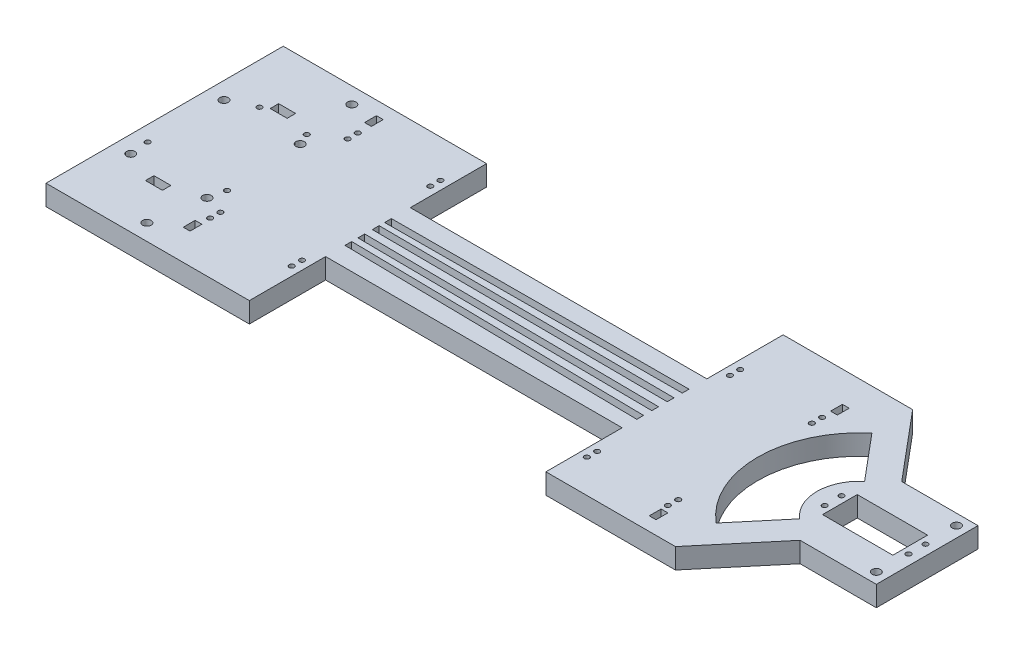
SolidWorks part; units mm, degrees
ref_plane "Front Plane" through (0, 0, 0) normal (0, 0, 1) x (1, 0, 0)
ref_plane "Top Plane" through (0, 0, 0) normal (0, 1, 0) x (1, 0, 0)
ref_plane "Right Plane" through (0, 0, 0) normal (1, 0, 0) x (0, 0, -1)
sketch "Sketch1" plane through (0, 0, 0) normal (0, 1, 0) x (1, 0, 0)
  line L0 (295, 140) -> (450, 140)
  line L1 (0, 0) -> (120, 0)
  line L2 (0, 0) -> (0, 140)
  line L3 (0, 140) -> (120, 140)
  line L4 (450, 0) -> (450, 140)
  line L6 (120, 140) -> (120, 95)
  line L7 (120, 95) -> (295, 95)
  line L8 (295, 140) -> (295, 95)
  line L10 (120, 0) -> (120, 45)
  line L11 (120, 45) -> (295, 45)
  line L12 (295, 0) -> (295, 45)
  line L13 (295, 0) -> (450, 0)
  line L14 (120, 83.84) -> (295, 84.455)
  line L15 (295, 84.455) -> (295, 80.455)
  line L16 (295, 80.455) -> (120, 79.84)
  line L17 (120, 79.84) -> (120, 83.84)
  line L18 (120, 76.59) -> (295, 75.595)
  line L19 (295, 75.595) -> (295, 71.595)
  line L20 (295, 71.595) -> (120, 72.59)
  line L21 (120, 72.59) -> (120, 76.59)
  line L22 (120, 68.09) -> (295, 66.495)
  line L23 (295, 66.495) -> (295, 62.495)
  line L24 (295, 62.495) -> (120, 64.09)
  line L25 (120, 64.09) -> (120, 68.09)
  line L26 (120, 60.42) -> (295, 57.635)
  line L27 (295, 57.635) -> (295, 53.635)
  line L28 (295, 53.635) -> (120, 56.42)
  line L29 (120, 56.42) -> (120, 60.42)
  line L30 (350, 140) -> (350, 0) construction
  line L31 (6.35, 104.3) -> (59.65, 104.3) construction
  line L32 (6.35, 104.3) -> (6.35, 35.7) construction
  line L33 (6.35, 35.7) -> (59.65, 35.7) construction
  line L34 (59.65, 104.3) -> (59.65, 35.7) construction
  line L35 (6, 112) -> (60, 112) construction
  line L36 (6, 112) -> (6, 28) construction
  line L37 (6, 28) -> (60, 28) construction
  line L38 (60, 112) -> (60, 28) construction
  line L39 (28, 104.3) -> (38, 104.3)
  line L40 (28, 104.3) -> (28, 109.3)
  line L41 (28, 109.3) -> (38, 109.3)
  line L42 (38, 104.3) -> (38, 109.3)
  line L43 (28, 35.7) -> (38, 35.7)
  line L44 (28, 35.7) -> (28, 30.7)
  line L45 (28, 30.7) -> (38, 30.7)
  line L46 (38, 35.7) -> (38, 30.7)
  line L47 (63, 132) -> (67, 132)
  line L48 (63, 132) -> (63, 125)
  line L49 (63, 125) -> (67, 125)
  line L50 (67, 132) -> (67, 125)
  line L51 (63, 25) -> (67, 25)
  line L52 (63, 25) -> (63, 18)
  line L53 (63, 18) -> (67, 18)
  line L54 (67, 25) -> (67, 18)
  line L56 (398.5, 80.25) -> (440, 80.25)
  line L57 (398.5, 80.25) -> (398.5, 59.75)
  line L58 (398.5, 59.75) -> (440, 59.75)
  line L59 (440, 80.25) -> (440, 59.75)
  line L60 (398.5, 80.25) -> (391.5, 80.25) construction
  line L61 (391.5, 80.25) -> (391.5, 59.75) construction
  line L62 (391.5, 59.75) -> (398.5, 59.75) construction
  line L63 (440, 59.75) -> (447, 59.75) construction
  line L64 (447, 59.75) -> (447, 80.25) construction
  line L65 (447, 80.25) -> (440, 80.25) construction
  line L66 (410, 80.25) -> (410, 59.75) construction
  line L67 (120, 81.84) -> (50119.6912, 257.5532) construction
  line L68 (393.9303, 50.8489) -> (371.4327, 24.0373)
  line L69 (393.9303, 89.1511) -> (371.4327, 115.9627)
  line L70 (120, 74.59) -> (50119.1918, -209.6911) construction
  line L71 (120, 66.09) -> (50117.9234, -389.6054) construction
  line L72 (120, 58.42) -> (50113.6696, -737.1935) construction
  line L73 (115.0463, 81.8226) -> (114.8605, 134.6962) construction
  line L74 (66.4466, 81.6518) -> (66.2773, 129.8225) construction
  line L75 (66.5944, 66.5768) -> (66.1224, 14.7918) construction
  line L76 (115.1924, 66.1338) -> (114.7306, 15.4677) construction
  line L77 (299.8782, 73.5673) -> (300.2267, 134.8495) construction
  line L78 (348.4774, 73.2909) -> (348.827, 134.7671) construction
  line L79 (300.1686, 55.5527) -> (299.5319, 15.545) construction
  line L80 (348.7624, 54.7794) -> (347.9619, 4.4785) construction
  line L82 (348, 122) -> (352, 122)
  line L83 (348, 122) -> (348, 115)
  line L84 (348, 115) -> (352, 115)
  line L85 (352, 122) -> (352, 115)
  line L86 (348, 15) -> (352, 15)
  line L87 (348, 15) -> (348, 8)
  line L88 (348, 8) -> (352, 8)
  line L89 (352, 15) -> (352, 8)
  circle A0 centre (8.95, 51) radius 1.5
  circle A1 centre (57.15, 49.7) radius 1.5
  circle A2 centre (24.15, 101.8) radius 1.5
  circle A3 centre (52.05, 101.8) radius 1.5
  circle A4 centre (50, 130.475) radius 2.5
  circle A5 centre (50, 9.525) radius 2.5
  circle A6 centre (10, 95) radius 2.5
  circle A7 centre (10, 40) radius 2.5
  circle A8 centre (55, 40) radius 2.5
  circle A9 centre (55, 95) radius 2.5
  arc A12 (371.4327, 115.9627) -> (371.4327, 24.0373) centre (410, 70) ccw
  arc A13 (393.9303, 89.1511) -> (393.9303, 50.8489) centre (410, 70) ccw
  circle A14 centre (394.5, 75) radius 1.5
  circle A15 centre (394.5, 65) radius 1.5
  circle A16 centre (444, 75) radius 1.5
  circle A17 centre (444, 65) radius 1.5
  circle A18 centre (114.9408, 111.8226) radius 1.5
  circle A19 centre (114.9198, 117.8226) radius 1.5
  circle A20 centre (66.3411, 111.6518) radius 1.5
  circle A21 centre (66.3201, 117.6518) radius 1.5
  circle A22 centre (114.919, 36.1338) radius 1.5
  circle A23 centre (114.8643, 30.1338) radius 1.5
  circle A24 centre (66.2663, 30.578) radius 1.5
  circle A25 centre (66.321, 36.578) radius 1.5
  circle A26 centre (300.0488, 103.5673) radius 1.5
  circle A27 centre (300.0829, 109.5673) radius 1.5
  circle A28 centre (348.6821, 109.2909) radius 1.5
  circle A29 centre (348.648, 103.2909) radius 1.5
  circle A30 centre (299.6911, 25.5527) radius 1.5
  circle A31 centre (299.5957, 19.5527) radius 1.5
  circle A32 centre (348.285, 24.7794) radius 1.5
  circle A33 centre (348.1895, 18.7794) radius 1.5
  point P27 (120, 81.84)
  point P30 (120, 74.59)
  point P31 (120, 66.09)
  point P32 (120, 58.42)
  point P33 (295, 82.455)
  point P35 (295, 73.595)
  point P36 (295, 64.495)
  point P37 (295, 55.635)
  point P41 (6.35, 70)
  point P46 (6, 70)
  point P47 (33, 28)
  point P50 (33, 35.7)
  point P61 (33, 112)
  point P62 (33, 109.3)
  point P79 (33, 30.7)
  point P88 (440, 70)
  point P121 (398.5, 70)
  point P156 (0, 0)
  dimension "D31" = 3
  dimension "D32" = 3
  dimension "D33" = 3
  dimension "D34" = 3
  dimension "D49" = 5
  dimension "D50" = 5
  dimension "D62" = 5
  dimension "D63" = 5
  dimension "D66" = 5
  dimension "D68" = 5
  dimension "D72" = 70
  dimension "D79" = 25
  dimension "D82" = 3
  dimension "D83" = 3
  dimension "D84" = 3
  dimension "D85" = 3
  dimension "D92" = 3
  dimension "D93" = 3
  dimension "D94" = 3
  dimension "D95" = 3
  dimension "D102" = 3
  dimension "D103" = 3
  dimension "D104" = 3
  dimension "D105" = 3
  dimension "D110" = 35
  dimension "D115" = 3
  dimension "D116" = 3
  dimension "D117" = 3
  dimension "D118" = 3
  dimension "D131" = 3
  dimension "D114" = 3
  dimension "D132" = 3
  dimension "D133" = 3
  dimension "D1" = 450
  dimension "D2" = 140
  dimension "D3" = 120
  dimension "D4" = 175
  dimension "D5" = 45
  dimension "D6" = 45
  dimension "D7" = 13.16
  dimension "D8" = 4
  dimension "D9" = 12.545
  dimension "D10" = 4
  dimension "D11" = 4
  dimension "D12" = 4
  dimension "D13" = 7.25
  dimension "D14" = 8.5
  dimension "D15" = 7.67
  dimension "D16" = 4
  dimension "D17" = 4
  dimension "D18" = 4
  dimension "D19" = 4
  dimension "D20" = 8.86
  dimension "D21" = 9.1
  dimension "D22" = 8.86
  dimension "D23" = 53.3
  dimension "D24" = 68.6
  dimension "D25" = 70
  dimension "D26" = 70
  dimension "D27" = 84
  dimension "D28" = 54
  dimension "D29" = 33
  dimension "D30" = 33
  dimension "D35" = 2.6
  dimension "D36" = 15.3
  dimension "D37" = 14
  dimension "D38" = 2.5
  dimension "D39" = 2.5
  dimension "D40" = 7.6
  dimension "D41" = 15.2
  dimension "D42" = 2.5
  dimension "D43" = 10
  dimension "D44" = 5
  dimension "D45" = 5
  dimension "D46" = 10
  dimension "D47" = 50
  dimension "D48" = 9.525
  dimension "D51" = 9.525
  dimension "D52" = 50
  dimension "D53" = 53
  dimension "D54" = 8
  dimension "D55" = 7
  dimension "D56" = 4
  dimension "D57" = 53
  dimension "D58" = 18
  dimension "D59" = 4
  dimension "D60" = 7
  dimension "D61" = 45
  dimension "D64" = 40
  dimension "D65" = 10
  dimension "D67" = 45
  dimension "D69" = 45
  dimension "D70" = 10
  dimension "D71" = 230
  dimension "D73" = 10
  dimension "D74" = 41.5
  dimension "D75" = 20.5
  dimension "D76" = 7
  dimension "D77" = 7
  dimension "D78" = 18.5
  dimension "D80" = 40
  dimension "D81" = 40
  dimension "D86" = 49.5
  dimension "D87" = 10
  dimension "D88" = 4
  dimension "D89" = 5
  dimension "D90" = 48.6
  dimension "D91" = 5
  dimension "D96" = 6
  dimension "D97" = 6
  dimension "D98" = 30
  dimension "D99" = 30
  dimension "D100" = 5
  dimension "D101" = 48.6
  dimension "D106" = 30
  dimension "D107" = 6
  dimension "D108" = 6
  dimension "D109" = 30
  dimension "D111" = 5
  dimension "D112" = 5
  dimension "D113" = 48.6
  dimension "D119" = 6
  dimension "D120" = 6
  dimension "D121" = 30
  dimension "D122" = 30
  dimension "D123" = 7
  dimension "D124" = 4
  dimension "D125" = 18
  dimension "D126" = 53
  dimension "D127" = 7
  dimension "D128" = 4
  dimension "D129" = 8
  dimension "D130" = 53
  dimension "D134" = 6
  dimension "D135" = 6
  dimension "D136" = 30
  dimension "D137" = 30
  dimension "D138" = 48.6
extrude "Boss-Extrude1" add sketch "Sketch1" along normal blind 12
sketch "Sketch2" plane through (0, 12, 0) normal (0, 1, 0) x (1, 0, 0)
  line L0 (371.4327, 140) -> (404.9967, 100)
  line L1 (450, 140) -> (295, 140) construction
  line L2 (450, 0) -> (450, 140) construction
  line L3 (393.9303, 89.1511) -> (371.4327, 115.9627) construction
  line L4 (371.4327, 0) -> (404.9967, 40)
  line L5 (295, 0) -> (450, 0) construction
  line L6 (371.4327, 24.0373) -> (393.9303, 50.8489) construction
  line L7 (450, 100) -> (404.9967, 100)
  line L8 (450, 40) -> (404.9967, 40)
  line L9 (371.4327, 140) -> (450, 140)
  line L10 (450, 140) -> (450, 100)
  line L11 (450, 40) -> (450, 0)
  line L12 (450, 0) -> (371.4327, 0)
  circle A0 centre (443.65, 93.65) radius 2.5
  circle A1 centre (443.65, 46.35) radius 2.5
  point P27 (0, 0)
  point P29 (439.1886, 100)
  dimension "D2" = 5
  dimension "D3" = 5
  dimension "D1" = 60
  dimension "D4" = 6.35
  dimension "D5" = 6.35
  dimension "D6" = 6.35
extrude "Cut-Extrude1" cut sketch "Sketch2" against normal through all
